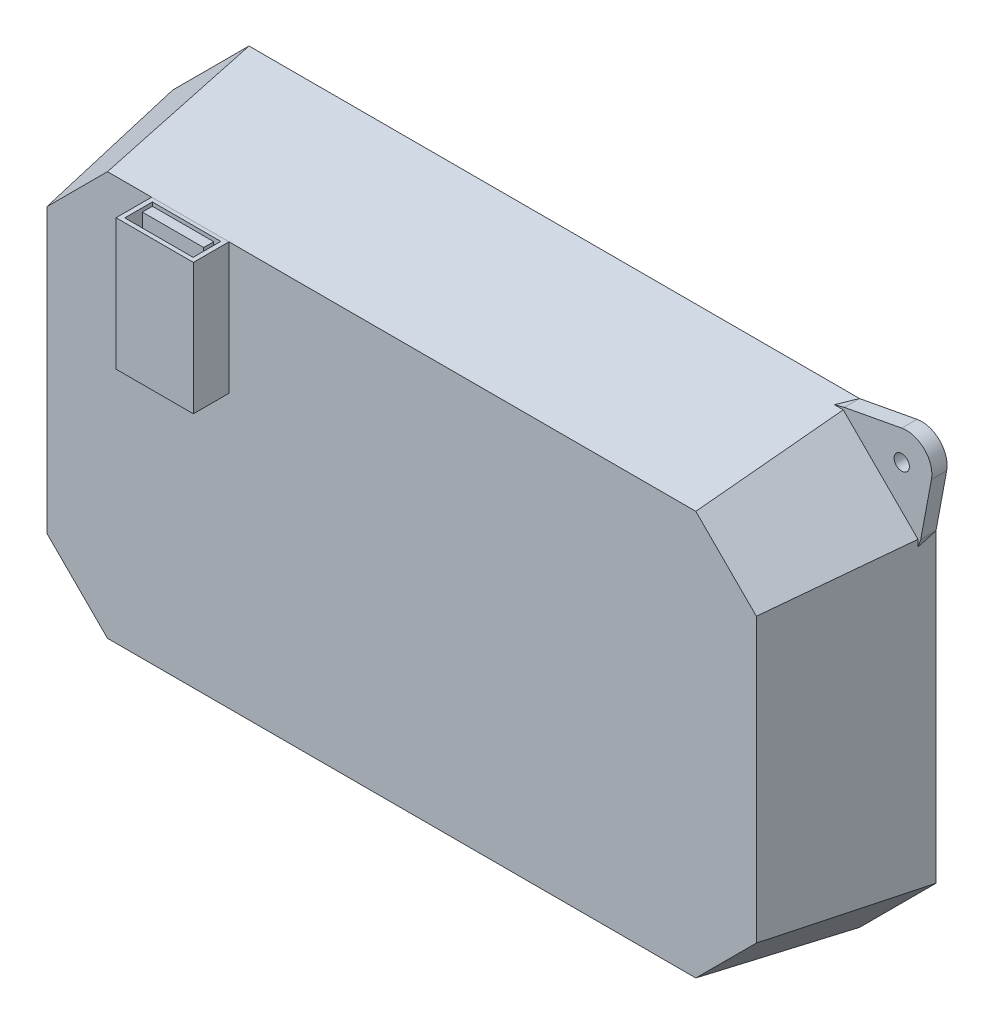
SolidWorks part; units mm, degrees
ref_plane "Front Plane" through (0, 0, 0) normal (0, 0, 1) x (1, 0, 0)
ref_plane "Top Plane" through (0, 0, 0) normal (0, 1, 0) x (1, 0, 0)
ref_plane "Right Plane" through (0, 0, 0) normal (1, 0, 0) x (0, 0, -1)
sketch "Sketch1" plane through (0, 0, 0) normal (0, 0, 1) x (1, 0, 0)
  line L0 (-100, 10.5319) -> (-85, 25.5319)
  line L1 (-85, 25.5319) -> (35, 25.5319)
  line L2 (-100, 10.5319) -> (-100, -49.4681)
  line L3 (-85, -64.4681) -> (35, -64.4681)
  line L4 (50, 10.5319) -> (50, -49.4681)
  line L5 (35, 25.5319) -> (50, 10.5319)
  line L6 (-100, -49.4681) -> (-85, -64.4681)
  line L7 (35, -64.4681) -> (50, -49.4681)
  point P0 (0, 0)
  point P1 (50, -64.4681)
  point P2 (-100, 25.5319)
  point P3 (-100, -64.4681)
  point P4 (50, 25.5319)
  dimension "D1" = 150
  dimension "D2" = 90
extrude "Boss-Extrude1" add sketch "Sketch1" along normal blind 30 draft 10
shell "Shell1" thickness 5
sketch "Sketch2" plane through (0, 0, 0) normal (0, 0, -1) x (-1, 0, 0)
  line L0 (-62.3182, -38.5412) -> (-17.6877, -80.1658)
  line L1 (16.2644, -18.1511) -> (30.5573, -17.7001) construction
  line L2 (-63.4472, -2.7551) -> (-21.5295, 41.6001)
  line L3 (25.1467, -3.7066) -> (25.5976, -17.9995) construction
  line L4 (114.6334, -32.9584) -> (72.7157, -77.3135)
  line L5 (113.5044, 2.8278) -> (68.874, 44.4523)
  line L6 (85, -64.4681) -> (-35, -64.4681) construction
  line L20 (-21.927, 54.2004) -> (-65.2011, 52.8351)
  line L21 (-65.2011, 52.8351) -> (-63.8358, 9.561)
  line L22 (-63.8358, 9.561) -> (-51.2354, 9.9586)
  line L23 (-51.2354, 9.9586) -> (-49.3292, -50.4598)
  line L24 (-49.3292, -50.4598) -> (-61.9296, -50.8573)
  line L25 (-61.9296, -50.8573) -> (-60.5643, -94.1314)
  line L26 (-60.5643, -94.1314) -> (-17.2902, -92.7661)
  line L27 (-17.2902, -92.7661) -> (-17.6877, -80.1658)
  line L28 (-17.6877, -80.1658) -> (72.7157, -77.3135)
  line L29 (72.7157, -77.3135) -> (73.1132, -89.9139)
  line L30 (73.1132, -89.9139) -> (116.3873, -88.5486)
  line L31 (116.3873, -88.5486) -> (115.022, -45.2745)
  line L32 (115.022, -45.2745) -> (102.4217, -45.672)
  line L33 (102.4217, -45.672) -> (100.5155, 14.7463)
  line L34 (100.5155, 14.7463) -> (113.1158, 15.1439)
  line L35 (113.1158, 15.1439) -> (111.7505, 58.4179)
  line L36 (111.7505, 58.4179) -> (68.4764, 57.0526)
  line L37 (68.4764, 57.0526) -> (68.874, 44.4523)
  line L38 (68.874, 44.4523) -> (-21.5295, 41.6001)
  line L39 (-21.5295, 41.6001) -> (-21.927, 54.2004)
  line L40 (-21.927, 54.2004) -> (-65.2011, 52.8351)
  line L41 (-65.2011, 52.8351) -> (-63.4472, -2.7551)
  line L45 (-62.3182, -38.5412) -> (-60.5643, -94.1314)
  line L46 (-60.5643, -94.1314) -> (-17.2902, -92.7661)
  line L47 (-17.2902, -92.7661) -> (-17.6877, -80.1658)
  line L49 (72.7157, -77.3135) -> (73.1132, -89.9139)
  line L50 (73.1132, -89.9139) -> (116.3873, -88.5486)
  line L51 (116.3873, -88.5486) -> (114.6334, -32.9584)
  line L55 (113.5044, 2.8278) -> (111.7505, 58.4179)
  line L56 (111.7505, 58.4179) -> (68.4764, 57.0526)
  line L57 (68.4764, 57.0526) -> (68.874, 44.4523)
  line L59 (-21.5295, 41.6001) -> (-21.927, 54.2004)
  dimension "D2" = 28.2981
  dimension "D1" = 0
sketch "Sketch4" plane through (0, 0, -43.692) normal (0, 0, -1) x (-1, 0, 0)
  circle A0 centre (-24.7585, -65.1412) radius 1.5
  point P2 (-30.6293, -65.264)
  point P3 (-33.6995, -61.9025)
  point P4 (-24.1074, -64.8849)
  point P5 (-24.7585, -65.1412)
  dimension "D1" = 3
ref_plane "Plane1" through (-25.0048, 0.7889, 0) normal (0.9995, -0.0315, 0) x (0, 0, -1)
ref_plane "Plane2" through (-0.5883, -18.6456, 0) normal (0.0315, 0.9995, 0) x (0.9995, -0.0315, 0)
sketch "Sketch6" plane through (0, 0, 30) normal (0, 0, 1) x (1, 0, 0)
  line L0 (32.8089, 20.2421) -> (-82.8089, 20.2421) construction
  line L1 (-74.1243, -5.5302) -> (-58.9267, -5.5302)
  line L2 (-74.1243, -5.5302) -> (-74.1243, 20.2421)
  line L3 (-74.1243, 20.2421) -> (-58.9267, 20.2421)
  line L4 (-58.9267, -5.5302) -> (-58.9267, 20.2421)
  line L5 (-74.1243, -5.5302) -> (-58.9267, 20.2421) construction
  line L6 (-74.1243, 20.2421) -> (-58.9267, -5.5302) construction
  point P0 (-66.5255, 7.356)
extrude "Boss-Extrude4" add sketch "Sketch6" along normal blind 7
sketch "Sketch7" plane through (0, 20.2421, 0) normal (0, 1, 0) x (1, 0, 0)
  line L1 (-73.2445, -30.7397) -> (-59.8107, -30.7397)
  line L2 (-73.2445, -30.7397) -> (-73.2445, -36.1685)
  line L3 (-73.2445, -36.1685) -> (-59.8107, -36.1685)
  line L4 (-59.8107, -30.7397) -> (-59.8107, -36.1685)
  line L5 (-72.5084, -31.4758) -> (-60.4548, -31.4758)
  line L6 (-72.5084, -31.4758) -> (-72.5084, -33.4541)
  line L7 (-72.5084, -33.4541) -> (-60.4548, -33.4541)
  line L8 (-60.4548, -31.4758) -> (-60.4548, -33.4541)
extrude "Cut-Extrude2" cut sketch "Sketch7" against normal blind 17
sketch "Sketch8" plane through (0, 0, 0) normal (0, 0, -1) x (-1, 0, 0)
  line L0 (-50, 10.5319) -> (-52.108, 21.8062)
  line L1 (-46.2742, 27.64) -> (-35, 25.5319)
  line L2 (-50, 10.5319) -> (-49.0622, 7.8499)
  line L3 (-49.0622, 7.8499) -> (-31.8453, 24.6824)
  line L5 (-31.8453, 24.6824) -> (-35, 25.5319)
  arc A0 (-52.108, 21.8062) -> (-46.2742, 27.64) centre (-47.1932, 22.7251) cw
  circle A1 centre (-46.2742, 21.8062) radius 1.5
  point P9 (-47.9408, 8.2399)
  point P12 (-31.8453, 24.6824)
  point P13 (-47.9408, 7.9149)
  point P14 (-49.0622, 7.8499)
  point P16 (-33.8549, 24.6179)
  line M10 (-35, 25.5319) -> (-50, 10.5319)
  dimension "D1" = 5
  dimension "D2" = 3
extrude "Boss-Extrude5" add sketch "Sketch8" against normal blind 3 separate body contours A0 L0 L1 A1 M10 | L3 L5 L2 M10
